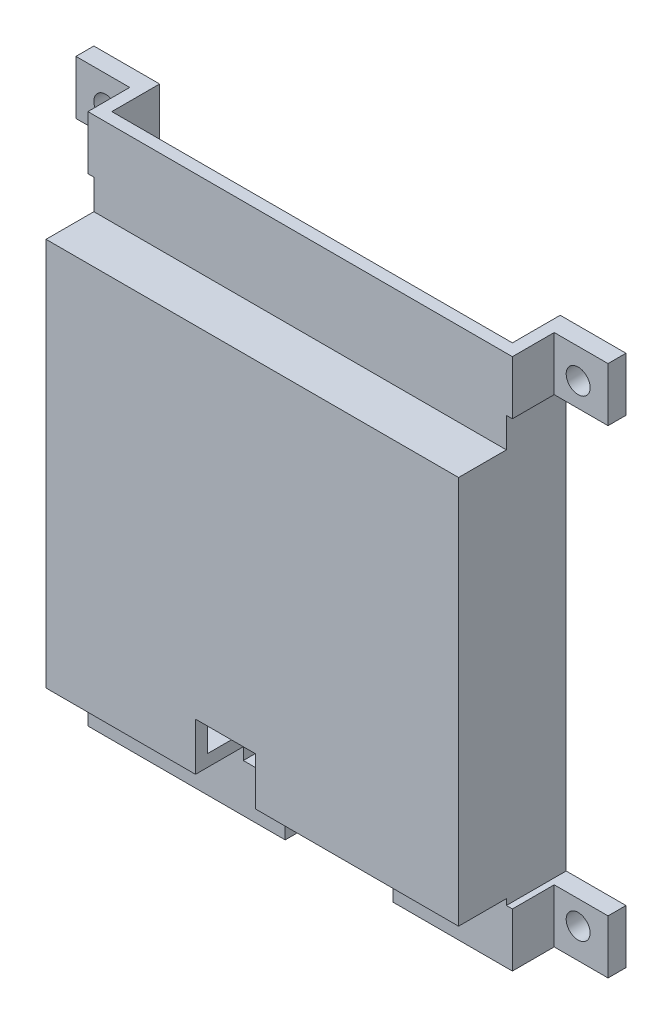
SolidWorks part; units mm, degrees
ref_plane "Front Plane" through (0, 0, 0) normal (0, 0, 1) x (1, 0, 0)
ref_plane "Top Plane" through (0, 0, 0) normal (0, 1, 0) x (1, 0, 0)
ref_plane "Right Plane" through (0, 0, 0) normal (1, 0, 0) x (0, 0, -1)
sketch "Esquisse1" plane through (0, 0, 0) normal (0, 0, 1) x (1, 0, 0)
  line L1 (-44.5, 44.5) -> (44.5, 44.5)
  line L2 (-44.5, 44.5) -> (-44.5, -44.5)
  line L3 (-44.5, -44.5) -> (44.5, -44.5)
  line L4 (44.5, 44.5) -> (44.5, -44.5)
  point P4 (-44.5, 0)
  point P6 (0, 44.5)
  dimension "D1" = 89
  dimension "D2" = 89
extrude "Main Extrusion" add sketch "Esquisse1" along normal blind 18
sketch "Esquisse2" plane through (0, 0, 18) normal (0, 0, 1) x (1, 0, 0)
  line L0 (44.5, 44.5) -> (-44.5, 44.5) construction
  line L1 (-44.5, 44.5) -> (-44.5, -44.5) construction
  line L2 (-44.5, -44.5) -> (44.5, -44.5) construction
  line L3 (44.5, -44.5) -> (44.5, 44.5) construction
  circle A0 centre (-39.5, 39.5) radius 2
  circle A1 centre (39.5, 39.5) radius 2
  circle A2 centre (39.5, -39.5) radius 2
  circle A3 centre (-39.5, -39.5) radius 2
  point P12 (0, 0)
  point P15 (0, 0)
  point P18 (0, 0)
  point P19 (0, 0)
  dimension "D1" = 4
  dimension "D2" = 5
  dimension "D3" = 5
  dimension "D4" = 5
  dimension "D5" = 5
extrude "Fixation Hole" cut sketch "Esquisse2" against normal through all
sketch "Esquisse3" plane through (0, 0, 18) normal (0, 0, 1) x (1, 0, 0)
  line L0 (44.5, -44.5) -> (44.5, 44.5) construction
  line L1 (-35.5, 35.5) -> (-44.5, 35.5)
  line L2 (-35.5, 35.5) -> (-35.5, 44.5)
  line L3 (-35.5, 44.5) -> (-44.5, 44.5)
  line L4 (-44.5, 35.5) -> (-44.5, 44.5)
  line L5 (-35.5, -35.5) -> (-44.5, -35.5)
  line L6 (-35.5, -35.5) -> (-35.5, -44.5)
  line L7 (-35.5, -44.5) -> (-44.5, -44.5)
  line L8 (-44.5, -35.5) -> (-44.5, -44.5)
  line L9 (35.5, -35.5) -> (44.5, -35.5)
  line L10 (35.5, -35.5) -> (35.5, -44.5)
  line L11 (35.5, -44.5) -> (44.5, -44.5)
  line L12 (44.5, -35.5) -> (44.5, -44.5)
  line L13 (-44.5, -44.5) -> (44.5, -44.5) construction
  line L14 (44.5, 44.5) -> (-44.5, 44.5) construction
  line L15 (35.5, 35.5) -> (44.5, 35.5)
  line L16 (35.5, 35.5) -> (35.5, 44.5)
  line L17 (35.5, 44.5) -> (44.5, 44.5)
  line L18 (44.5, 35.5) -> (44.5, 44.5)
  point P4 (-44.5, 44.5)
  point P25 (-41.0041, 40.8182)
  point P26 (-38.0018, 40.8249)
  dimension "D2" = 9
extrude "Fixation Square" cut sketch "Esquisse3" against normal blind 15
sketch "Esquisse4" plane through (0, 0, 0) normal (0, 0, -1) x (-1, 0, 0)
  line L0 (-44.5, -44.5) -> (-44.5, 44.5) construction
  line L2 (44.5, 35.5) -> (44.5, -35.5) construction
  line L3 (-35.5, 44.5) -> (35.5, 44.5) construction
  line L5 (-32.5, -32.5) -> (-15.5, -32.5)
  line L6 (-32.5, 28.5) -> (-32.5, -32.5)
  line L8 (-15.5, -32.5) -> (-15.5, -44.5)
  line L9 (32.5, -32.5) -> (32.5, 28.5)
  line L10 (44.5, -44.5) -> (-44.5, -44.5) construction
  line L11 (-15.5, -44.5) -> (2.5, -44.5)
  line L12 (2.5, -44.5) -> (2.5, -32.5)
  line L13 (2.5, -32.5) -> (32.5, -32.5)
  line L14 (44.5, 44.5) -> (44.5, -44.5) construction
  line L15 (32.5, 28.5) -> (-32.5, 28.5)
  dimension "D1" = 12
  dimension "D2" = 12
  dimension "D3" = 16
  dimension "D4" = 12
  dimension "D5" = 42
  dimension "D6" = 18
extrude "CPU + RJ11" cut sketch "Esquisse4" against normal blind 16
sketch "Esquisse5" plane through (0, 0, 18) normal (0, 0, 1) x (1, 0, 0)
  line L0 (-35.5, -35.5) -> (-44.5, -35.5) construction
  line L1 (-44.5, 35.5) -> (-34.5, 35.5)
  line L2 (-44.5, 35.5) -> (-44.5, -35.5)
  line L3 (-44.5, -35.5) -> (-34.5, -35.5)
  line L4 (-34.5, 35.5) -> (-34.5, -35.5)
  line L5 (44.5, 35.5) -> (34.5, 35.5)
  line L6 (44.5, 35.5) -> (44.5, -35.5)
  line L7 (44.5, -35.5) -> (34.5, -35.5)
  line L8 (34.5, 35.5) -> (34.5, -35.5)
  line L9 (44.5, -35.5) -> (44.5, 35.5) construction
  line L10 (44.5, -35.5) -> (35.5, -35.5) construction
  point P28 (33.5, -43.7735)
  point P29 (33.5, -55.3276)
  point P30 (33.5, -45.3794)
  point P31 (33.5, -44.5)
  point P34 (32.8887, 44.5)
  dimension "D1" = 10
  dimension "D2" = 10
extrude "Enlèv. mat.-Extru.4" cut sketch "Esquisse5" against normal through all
sketch "Esquisse6" plane through (0, 0, 0) normal (0, 0, -1) x (-1, 0, 0)
  line L0 (-44.5, 44.5) -> (44.5, 44.5) construction
  line L1 (-33.5, 44.5) -> (33.5, 44.5)
  line L2 (-33.5, 44.5) -> (-33.5, 30.5)
  line L3 (-33.5, 30.5) -> (33.5, 30.5)
  line L4 (33.5, 44.5) -> (33.5, 30.5)
  line L5 (44.5, 44.5) -> (44.5, 35.5) construction
  line L6 (-44.5, 35.5) -> (-44.5, 44.5) construction
  line L8 (-17.5, -33.5) -> (-33.5, -33.5)
  line L9 (-17.5, -33.5) -> (-17.5, -44.5)
  line L10 (-17.5, -44.5) -> (-33.5, -44.5)
  line L11 (-33.5, -33.5) -> (-33.5, -44.5)
  line L12 (-15.5, -44.5) -> (-44.5, -44.5) construction
  line L13 (44.5, -44.5) -> (2.5, -44.5) construction
  line L14 (33.5, -33.5) -> (4.5, -33.5)
  line L15 (33.5, -33.5) -> (33.5, -44.5)
  line L16 (33.5, -44.5) -> (4.5, -44.5)
  line L17 (4.5, -33.5) -> (4.5, -44.5)
  line L18 (34.5, -35.5) -> (34.5, 35.5) construction
  line L21 (-15.5, -32.5) -> (-15.5, -44.5) construction
  line L22 (2.5, -44.5) -> (2.5, -32.5) construction
  point P14 (-19.0995, -44.5)
  point P27 (-15.5, -38.5)
  dimension "D1" = 11
  dimension "D2" = 11
  dimension "D3" = 14
  dimension "D4" = 1
  dimension "D5" = 11
  dimension "D6" = 2
  dimension "D7" = 2
extrude "HE10 Connectors" cut sketch "Esquisse6" against normal blind 8
sketch "Esquisse7" plane through (-35.5, 0, 0) normal (-1, 0, 0) x (0, 0, 1)
  line L1 (18, 44.5) -> (10, 44.5)
  line L2 (18, 44.5) -> (18, 30.5)
  line L3 (18, 30.5) -> (10, 30.5)
  line L4 (10, 44.5) -> (10, 30.5)
  line L5 (18, -44.5) -> (10, -44.5)
  line L6 (18, -44.5) -> (18, -34.5)
  line L7 (18, -34.5) -> (10, -34.5)
  line L8 (10, -44.5) -> (10, -34.5)
  dimension "D1" = 8
  dimension "D2" = 14
  dimension "D3" = 10
extrude "HE10 Connectors Top" cut sketch "Esquisse7" against normal through all
sketch "Esquisse9" plane through (0, 0, 18) normal (0, 0, 1) x (1, 0, 0)
  line L0 (-44.5, -35.5) -> (-44.5, -44.5) construction
  line L1 (-9.5, -26.5) -> (0.5, -26.5)
  line L2 (-9.5, -26.5) -> (-9.5, -36.5)
  line L3 (-9.5, -36.5) -> (0.5, -36.5)
  line L4 (0.5, -26.5) -> (0.5, -36.5)
  line L5 (-35.5, -44.5) -> (35.5, -44.5) construction
  dimension "D1" = 35
  dimension "D2" = 8
  dimension "D3" = 10
  dimension "D4" = 10
extrude "Enlèv. mat.-Extru.7" cut sketch "Esquisse9" against normal through all and the other way through all
